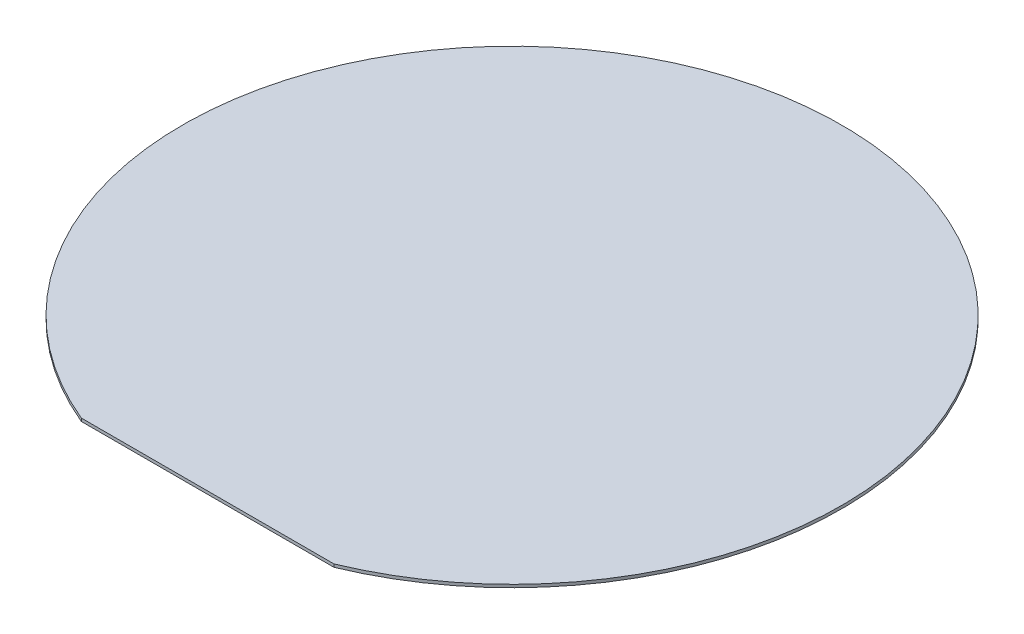
SolidWorks part; units mm, degrees
material "Silicon"
ref_plane "Front Plane" through (0, 0, 0) normal (0, 0, 1) x (1, 0, 0)
ref_plane "Top Plane" through (0, 0, 0) normal (0, 1, 0) x (1, 0, 0)
ref_plane "Right Plane" through (0, 0, 0) normal (1, 0, 0) x (0, 0, -1)
sketch "Sketch1" plane through (0, 0, 0) normal (0, 1, 0) x (1, 0, 0)
  circle A0 centre (0, 0) radius 75
  dimension "D1" = 150
extrude "Boss-Extrude1" add sketch "Sketch1" along normal blind 0.675
sketch "Sketch2" plane through (0, 0.675, 0) normal (0, 1, 0) x (1, 0, 0)
  line L0 (0, 0) -> (0, -98.7127) construction
  line L1 (-28.75, -69.2708) -> (28.75, -69.2708)
  line L2 (-28.75, -69.2708) -> (-28.75, -97.5009)
  line L3 (-28.75, -97.5009) -> (28.75, -97.5009)
  line L4 (28.75, -69.2708) -> (28.75, -97.5009)
  line L5 (-28.75, -69.2708) -> (28.75, -97.5009) construction
  line L6 (-28.75, -97.5009) -> (28.75, -69.2708) construction
  circle A0 centre (0, 0) radius 75 construction
  point P0 (0, -83.3858)
  point P8 (0, 0)
  dimension "D1" = 0
  dimension "D2" = 57.5
extrude "Cut-Extrude1" cut sketch "Sketch2" against normal blind 0.675
